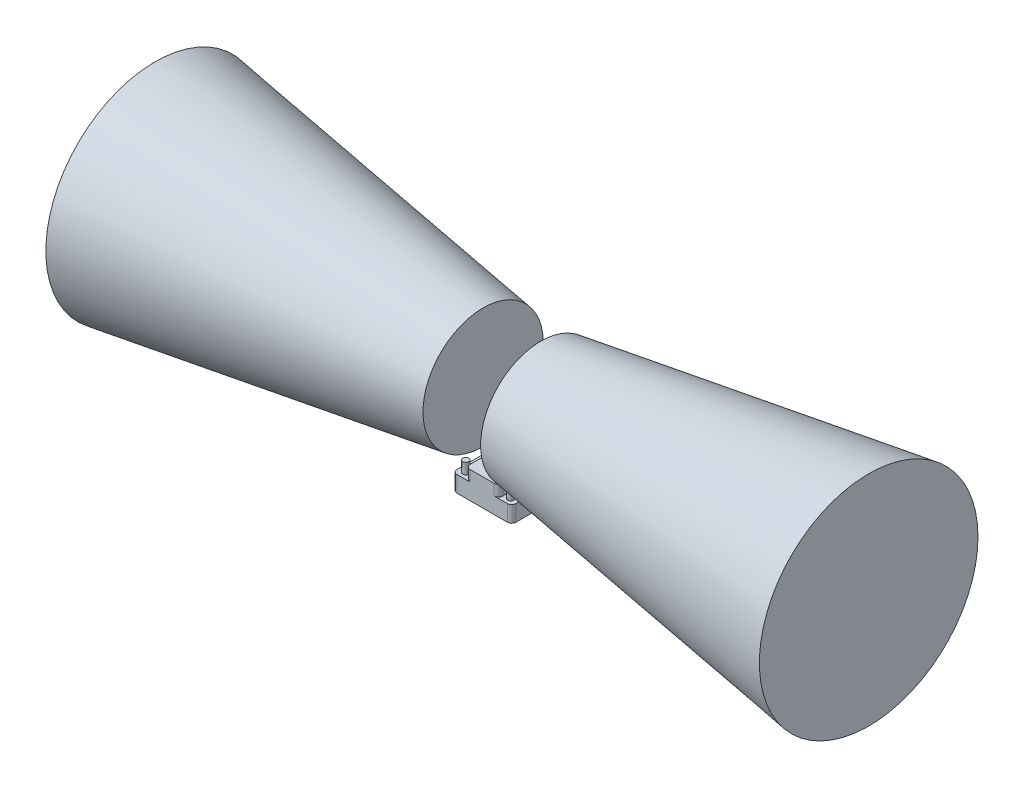
SolidWorks part; units mm, degrees
ref_plane "Front Plane" through (0, 0, 0) normal (0, 0, 1) x (1, 0, 0)
ref_plane "Top Plane" through (0, 0, 0) normal (0, 1, 0) x (1, 0, 0)
ref_plane "Right Plane" through (0, 0, 0) normal (1, 0, 0) x (0, 0, -1)
sketch "Sketch1" plane through (0, 0, 0) normal (0, 1, 0) x (1, 0, 0)
  line L1 (-23, -37.25) -> (23, -37.25)
  line L2 (-27, -33.25) -> (-27, 33.25)
  line L3 (-23, 37.25) -> (23, 37.25)
  line L4 (27, -33.25) -> (27, 33.25)
  line L5 (-27, -37.25) -> (27, 37.25) construction
  line L6 (-27, 37.25) -> (27, -37.25) construction
  arc A0 (-23, -37.25) -> (-27, -33.25) centre (-23, -33.25) cw
  arc A1 (23, -37.25) -> (27, -33.25) centre (23, -33.25) ccw
  arc A2 (23, 37.25) -> (27, 33.25) centre (23, 33.25) cw
  arc A3 (-27, 33.25) -> (-23, 37.25) centre (-23, 33.25) cw
  point P0 (0, 0)
  dimension "D3" = 4
  dimension "D1" = 74.5
  dimension "D2" = 54
extrude "Boss-Extrude1" add sketch "Sketch1" along normal blind 4.8 and the other way blind 10
sketch "Sketch2" plane through (0, 4.8, 0) normal (0, 1, 0) x (1, 0, 0)
  line L0 (23, 37.25) -> (-23, 37.25) construction
  line L1 (-11, -37.25) -> (11, -37.25)
  line L2 (-15, -33.25) -> (-15, 33.25)
  line L3 (-11, 37.25) -> (11, 37.25)
  line L4 (15, -33.25) -> (15, 33.25)
  line L5 (-15, -37.25) -> (15, 37.25) construction
  line L6 (-15, 37.25) -> (15, -37.25) construction
  line L7 (17.8, -31.625) -> (-17.8, -31.625) construction
  line L12 (23.3, 31.625) -> (-23.3, 31.625) construction
  line L13 (0, -31.625) -> (0, 31.625) construction
  arc A0 (-11, -37.25) -> (-15, -33.25) centre (-11, -33.25) cw
  arc A1 (11, -37.25) -> (15, -33.25) centre (11, -33.25) ccw
  arc A2 (11, 37.25) -> (15, 33.25) centre (11, 33.25) cw
  arc A3 (-15, 33.25) -> (-11, 37.25) centre (-11, 33.25) cw
  circle A4 centre (20.55, -31.625) radius 2.75
  circle A5 centre (-20.55, -31.625) radius 2.75
  circle A6 centre (-20.55, 21.625) radius 2.75
  circle A7 centre (-20.55, 31.625) radius 2.75 construction
  circle A8 centre (20.55, 21.625) radius 2.75
  circle A9 centre (20.55, 31.625) radius 2.75 construction
  point P0 (0, 0)
  point P42 (0, -31.625)
  dimension "D2" = 4
  dimension "D1" = 30
extrude "Boss-Extrude2" add sketch "Sketch2" along normal blind 10
sketch3d "3DSketch1"
  line L0 (-23, 0, 37.25) -> (23, 0, 37.25)
  line L1 (-23, -10, 37.25) -> (-23, 4.8, 37.25) construction
  line L2 (23, -10, 37.25) -> (23, 4.8, 37.25) construction
  line L3 (-23, 4.8, 37.25) -> (-11, 4.8, 37.25) construction
  line L4 (23, 0, -37.25) -> (-23, 0, -37.25)
  line L5 (23, -10, -37.25) -> (23, 4.8, -37.25) construction
  line L6 (-23, -10, -37.25) -> (-23, 4.8, -37.25) construction
  line L7 (23, 4.8, -37.25) -> (11, 4.8, -37.25) construction
  dimension "D1" = 4.8
  dimension "D2" = 4.8
ref_plane "Plane1" through (0, 0, 10) normal (0, 0, 1) x (1, 0, 0)
sketch "Sketch3" plane through (0, 0, 10) normal (0, 0, 1) x (1, 0, 0)
  line L1 (0, 0) -> (0, 94) construction
  line L3 (26.3746, 121.5) -> (326.3746, 166.5)
  line L4 (326.3746, 166.5) -> (326.3746, 66.5)
  line L5 (26.3746, 66.5) -> (326.3746, 66.5)
  line L11 (26.3746, 66.5) -> (26.3746, 121.5)
  line L12 (-26.3746, 66.5) -> (-26.3746, 121.5)
  line L13 (-26.3746, 66.5) -> (-326.3746, 66.5)
  line L14 (-326.3746, 166.5) -> (-326.3746, 66.5)
  line L15 (-26.3746, 121.5) -> (-326.3746, 166.5)
  point P8 (26.3746, 94)
  dimension "D1" = 300
  dimension "D2" = 94
  dimension "D4" = 100
  dimension "D5" = 55
revolve "Revolve2" add sketch "Sketch3" angle 360 about L13
